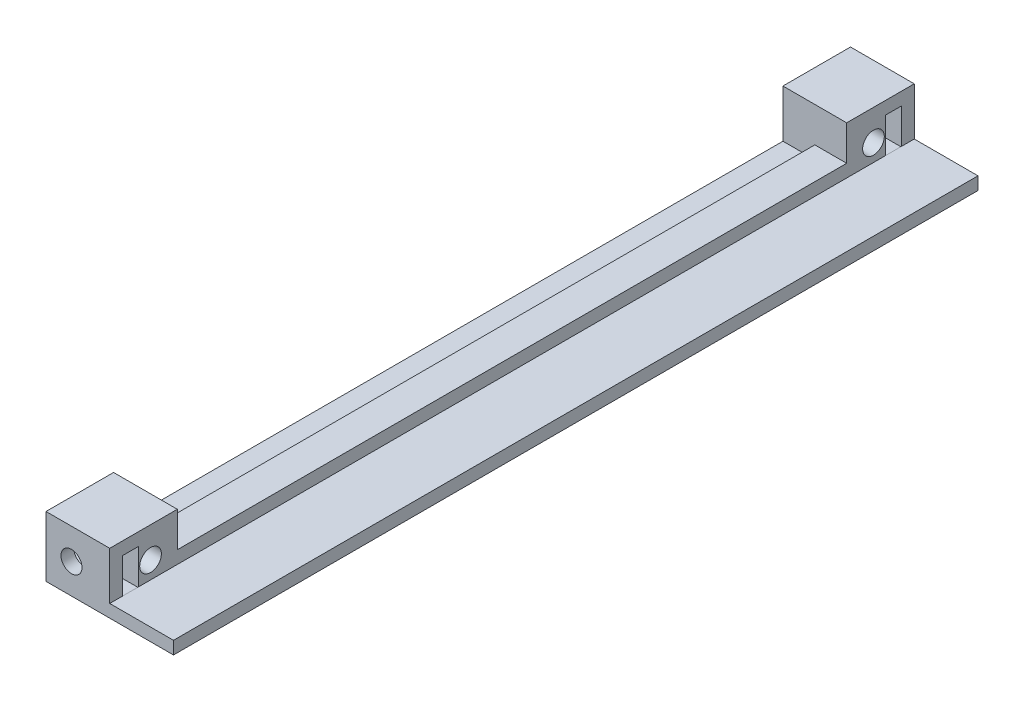
SolidWorks part; units mm, degrees
ref_plane "Plano frontal" through (0, 0, 0) normal (0, 0, 1) x (1, 0, 0)
ref_plane "Plano superior" through (0, 0, 0) normal (0, 1, 0) x (1, 0, 0)
ref_plane "Plano direito" through (0, 0, 0) normal (1, 0, 0) x (0, 0, -1)
sketch "Esboço1" plane through (0, 0, 0) normal (0, 0, 1) x (1, 0, 0)
  line L0 (0, 0) -> (0, 2)
  line L1 (0, 2) -> (5, 2)
  line L2 (5, 2) -> (5, 4)
  line L3 (5, 4) -> (10, 4)
  line L4 (10, 4) -> (10, 2)
  line L5 (20, 0) -> (0, 0)
  line L6 (10, 2) -> (20, 2)
  line L7 (20, 2) -> (20, 0)
  dimension "D1" = 2
  dimension "D2" = 2
  dimension "D3" = 5
  dimension "D4" = 5
  dimension "D5" = 10
extrude "Ressalto-extrusão1" add sketch "Esboço1" along normal mid plane 105
sketch "Esboço3" plane through (0, 0, 52.5) normal (0, 0, 1) x (1, 0, 0)
  line L1 (0, 0) -> (10, 0)
  line L2 (0, 0) -> (0, 4)
  line L3 (0, 4) -> (10, 4)
  line L4 (10, 0) -> (10, 4)
extrude "Ressalto-extrusão2" add sketch "Esboço3" against normal blind 5
sketch "Esboço4" plane through (10, 0, 0) normal (1, 0, 0) x (0, 0, -1)
  line L0 (-52.5, 9.5) -> (-63.1, 9.5)
  line L1 (-52.5, 9.5) -> (-52.5, 3.7429)
  line L2 (-63.1, 0) -> (-52.5, 0)
  line L4 (2.5, 0) -> (2.5, 21.5057) construction
  line L5 (-47.5, 0) -> (52.5, 0) construction
  line L6 (-63.1, 9.5) -> (-63.1, 0)
  line L8 (-61.1, 7.5) -> (-58.6, 7.5)
  line L9 (-52.5, 3.7429) -> (-52.5, 0)
  line L10 (-61.1, 7.5) -> (-61.1, 1.9)
  line L11 (-61.1, 1.9) -> (-58.6, 1.9)
  line L12 (-58.6, 7.5) -> (-58.6, 1.9)
  line L13 (-61.1, 7.5) -> (-58.6, 1.9) construction
  line L14 (-61.1, 1.9) -> (-58.6, 7.5) construction
  circle A0 centre (-56.7, 4.7) radius 1.7
  point P0 (-105, 0)
  point P4 (0, 0)
  point P7 (-106.4656, 8.3439)
  point P14 (-59.85, 4.7)
  point P22 (-116.5265, 8.4)
  point P23 (-109.0163, 8.4)
  point P24 (-115, 3.8609)
  dimension "D1" = 3.4
  dimension "D2" = 2
  dimension "D3" = 2.5
  dimension "D4" = 3
  dimension "D5" = 0.2
  dimension "D6" = 5.6
  dimension "D7" = 2.5
  dimension "D8" = 2
extrude "Ressalto-extrusão3" add sketch "Esboço4" against normal through all
sketch "Esboço5" plane through (0, 0, 63.1) normal (0, 0, 1) x (1, 0, 0)
  line L0 (0, 7.5) -> (0, 1.9) construction
  line L1 (0, 7.5) -> (0, 1.9) construction
  circle A0 centre (4, 4.7) radius 1.65
  point P4 (0, 4.7)
  point P5 (0, 0)
  dimension "D2" = 3.3
  dimension "D1" = 4
extrude "Corte-extrusão1" cut sketch "Esboço5" against normal blind 6
mirror "Espelhar1" about plane through (0, 0, 0) normal (0, 0, 1) of "Corte-extrusão1", "Ressalto-extrusão3"
sketch "Esboço6" plane through (0, 0, 52.5) normal (0, 0, 1) x (1, 0, 0)
  line L4 (10, 2) -> (10, 0)
  line L5 (10, 0) -> (20, 0)
  line L6 (20, 0) -> (20, 2)
  line L7 (20, 2) -> (10, 2)
  line L8 (10, 2) -> (10, 0)
  line L9 (10, 0) -> (20, 0)
  line L10 (20, 0) -> (20, 2)
  line L11 (20, 2) -> (10, 2)
  dimension "D1" = 0
extrude "Ressalto-extrusão4" add sketch "Esboço6" along normal up to surface and the other way up to surface up to face at (5.65, 4.7, 63.1) other way up to face at (5.65, 4.7, -63.1)
